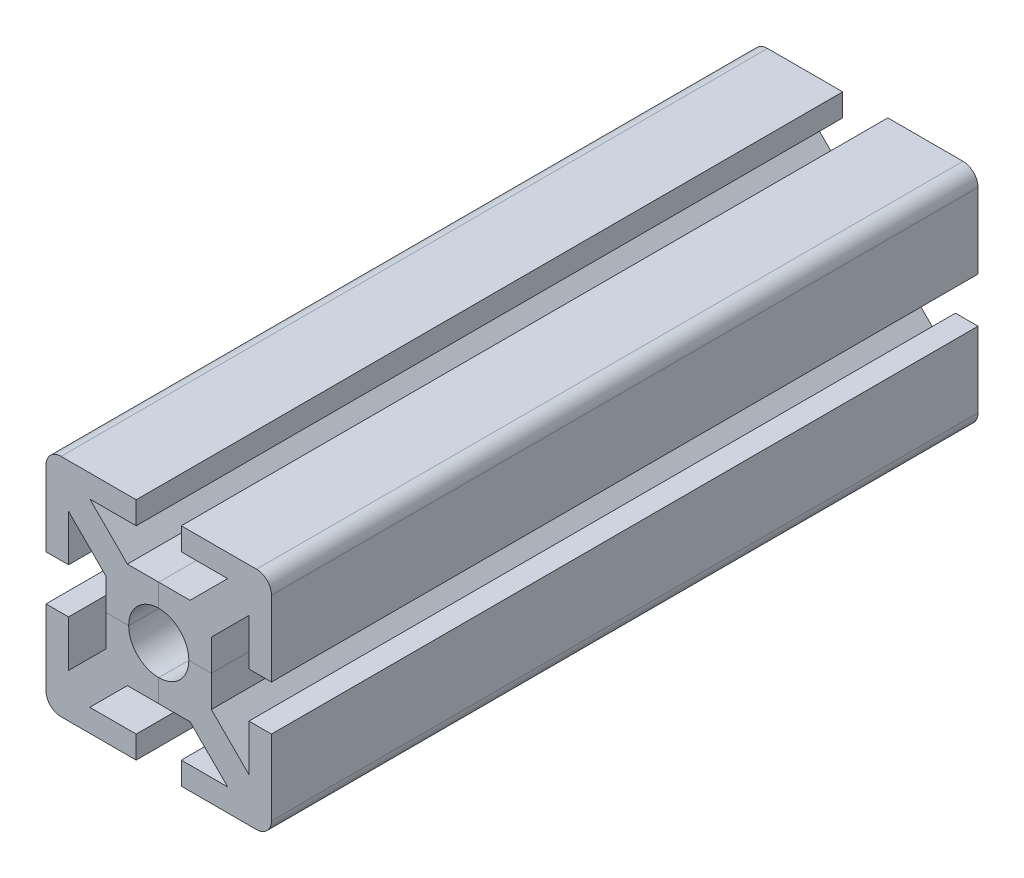
SolidWorks part; units mm, degrees
ref_plane "Alzado" through (0, 0, 0) normal (0, 0, 1) x (1, 0, 0)
ref_plane "Planta" through (0, 0, 0) normal (0, 1, 0) x (1, 0, 0)
ref_plane "Vista lateral" through (0, 0, 0) normal (1, 0, 0) x (0, 0, -1)
sketch "Croquis1" plane through (0, 0, 0) normal (0, 0, 1) x (1, 0, 0)
  line L0 (0, 0) -> (50000, 0) construction
  line L1 (-15, 15) -> (15, 15) construction
  line L2 (-15, 15) -> (-15, -15) construction
  line L3 (-15, -15) -> (15, -15) construction
  line L4 (15, 15) -> (15, -15) construction
  line L5 (-15, 15) -> (15, -15) construction
  line L6 (-15, -15) -> (15, 15) construction
  line L7 (0, 0) -> (0, -50000) construction
  line L8 (0, 4) -> (0, 7)
  line L9 (0, 7) -> (4.1716, 7)
  line L10 (4.1716, 7) -> (9.1716, 12)
  line L11 (9.1716, 12) -> (3, 12)
  line L12 (3, 12) -> (3, 15)
  line L13 (3, 15) -> (15, 15)
  line L20 (2.8284, 2.8284) -> (15, 15)
  arc A0 (2.8284, 2.8284) -> (0, 4) centre (0, 0) ccw
  point P0 (0, 0)
  dimension "D3" = 4
  dimension "D1" = 30
  dimension "D2" = 6
  dimension "D4" = 8
  dimension "D5" = 3
  dimension "D6" = 2
extrude "Saliente-Extruir1" add sketch "Croquis1" along normal mid plane 94
mirror "Simetría1" about plane through (2.8284, 2.8284, 47) normal (-0.7071, 0.7071, 0) of "Saliente-Extruir1"
fillet "Redondeo1" radius 2 1 edges at (15, 15, 0)
pattern_circular "MatrizC4" count 4 over 360 about axis through (0, 0, 0) along (0, 0, 1) of bodies 102
